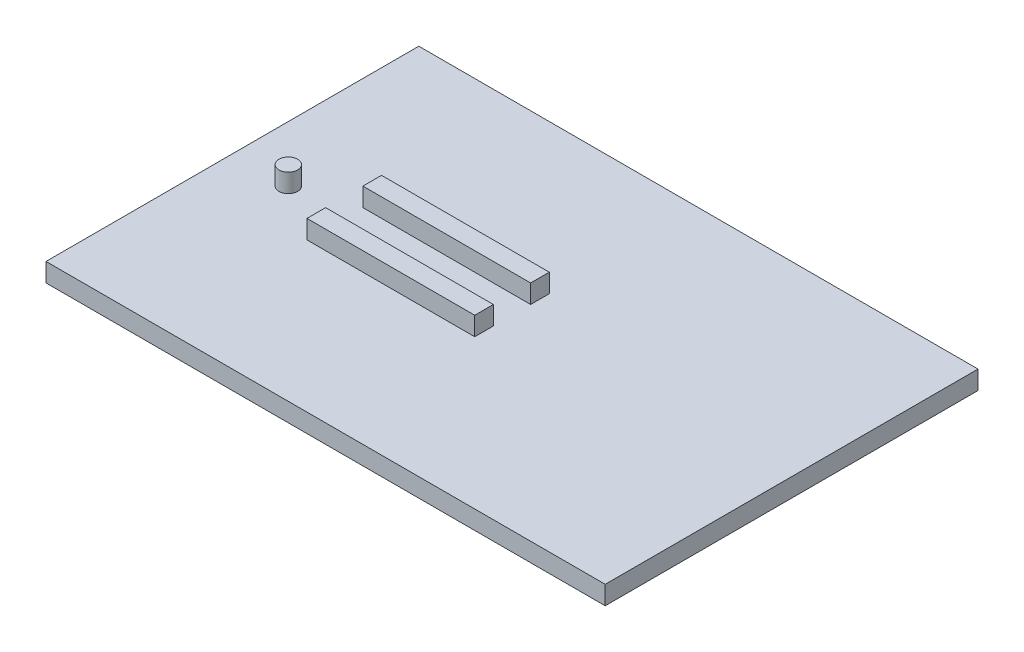
SolidWorks part; units mm, degrees
ref_plane "Front Plane" through (0, 0, 0) normal (0, 0, 1) x (1, 0, 0)
ref_plane "Top Plane" through (0, 0, 0) normal (0, 1, 0) x (1, 0, 0)
ref_plane "Right Plane" through (0, 0, 0) normal (1, 0, 0) x (0, 0, -1)
sketch "Sketch1" plane through (0, 0, 0) normal (0, 1, 0) x (1, 0, 0)
  line L1 (0, 0) -> (300, 0)
  line L2 (0, 0) -> (0, 200)
  line L3 (0, 200) -> (300, 200)
  line L4 (300, 0) -> (300, 200)
  dimension "D1" = 200
  dimension "D2" = 300
extrude "Boss-Extrude1" add sketch "Sketch1" along normal blind 10
sketch "Sketch2" plane through (0, 10, 0) normal (0, 1, 0) x (1, 0, 0)
  line L0 (0, 200) -> (0, 0) construction
  line L1 (105, 110) -> (105, 90) construction
  line L2 (60, 110) -> (150, 110)
  line L3 (60, 110) -> (60, 120)
  line L4 (60, 120) -> (150, 120)
  line L5 (150, 110) -> (150, 120)
  line L6 (60, 90) -> (150, 90)
  line L7 (60, 90) -> (60, 80)
  line L8 (60, 80) -> (150, 80)
  line L9 (150, 90) -> (150, 80)
  circle A0 centre (30, 100) radius 5
  point P2 (0, 100)
  point P15 (105, 100)
  dimension "D1" = 10
  dimension "D2" = 30
  dimension "D3" = 20
  dimension "D4" = 90
  dimension "D5" = 30
  dimension "D6" = 10
extrude "Boss-Extrude2" add sketch "Sketch2" along normal blind 10
